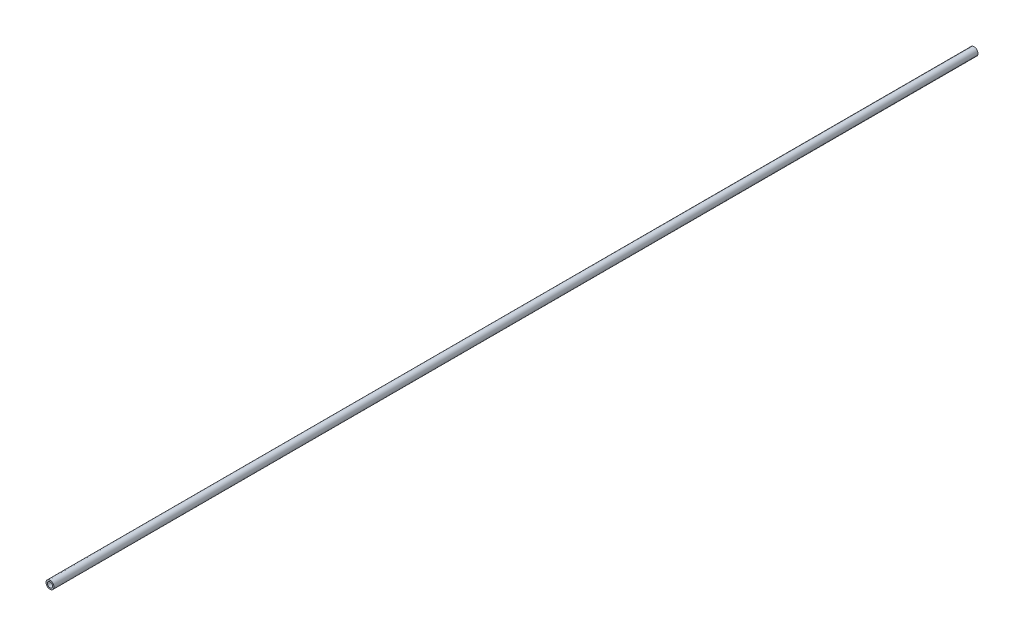
SolidWorks part; units mm, degrees
ref_plane "Front Plane" through (0, 0, 0) normal (0, 0, 1) x (1, 0, 0)
ref_plane "Top Plane" through (0, 0, 0) normal (0, 1, 0) x (1, 0, 0)
ref_plane "Right Plane" through (0, 0, 0) normal (1, 0, 0) x (0, 0, -1)
sketch "Sketch1" plane through (0, 0, 0) normal (0, 0, 1) x (1, 0, 0)
  circle A0 centre (0, 0) radius 1.5
  circle A1 centre (0, 0) radius 1
  dimension "D1" = 3
  dimension "D2" = 2
extrude "tail_rod_extrude" add sketch "Sketch1" along normal blind 350
